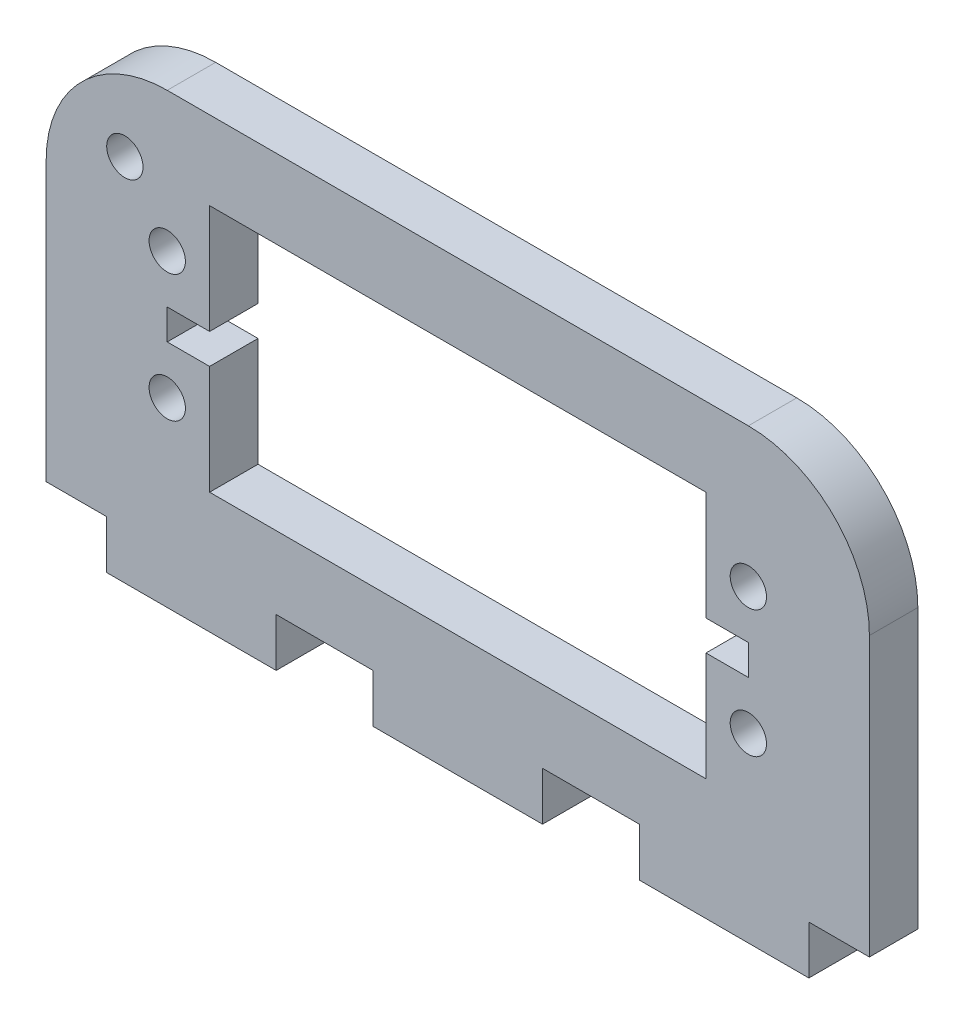
SolidWorks part; units mm, degrees
material "Beech"
ref_plane "Front Plane" through (0, 0, 0) normal (0, 0, 1) x (1, 0, 0)
ref_plane "Top Plane" through (0, 0, 0) normal (0, 1, 0) x (1, 0, 0)
ref_plane "Right Plane" through (0, 0, 0) normal (1, 0, 0) x (0, 0, -1)
sketch "Sketch1" plane through (0, 0, 0) normal (0, 0, 1) x (1, 0, 0)
  line L0 (49, 4) -> (49, 0)
  line L1 (19, 4) -> (19, 0)
  line L2 (41, 4) -> (41, 0)
  line L3 (41, 0) -> (27, 0)
  line L4 (27, 0) -> (27, 4)
  line L5 (63, 0) -> (49, 0)
  line L6 (19, 0) -> (5, 0)
  line L7 (63, 4) -> (63, 0)
  line L8 (5, 4) -> (5, 0)
  line L9 (63, 4) -> (68, 4)
  line L10 (5, 4) -> (0, 4)
  line L11 (54.5, 30.5) -> (54.5, 21.5)
  line L12 (13.5, 30.5) -> (54.5, 30.5)
  line L13 (13.5, 10) -> (13.5, 19)
  line L14 (54.5, 10) -> (13.5, 10)
  line L15 (10, 21.5) -> (10, 19)
  line L16 (10, 19) -> (13.5, 19)
  line L17 (10, 21.5) -> (13.5, 21.5)
  line L18 (58, 21.5) -> (58, 19)
  line L19 (58, 19) -> (54.5, 19)
  line L20 (58, 21.5) -> (54.5, 21.5)
  line L21 (54.5, 19) -> (54.5, 10)
  line L22 (13.5, 21.5) -> (13.5, 30.5)
  line L23 (19, 4) -> (27, 4)
  line L24 (41, 4) -> (49, 4)
  line L25 (68, 4) -> (68, 27)
  line L26 (58, 37) -> (10, 37)
  line L27 (0, 27) -> (0, 4)
  circle A0 centre (10, 15) radius 1.5
  circle A1 centre (10, 25.5) radius 1.5
  circle A2 centre (58, 15) radius 1.5
  circle A3 centre (58, 25.5) radius 1.5
  arc A4 (68, 27) -> (58, 37) centre (58, 27) ccw
  arc A5 (10, 37) -> (0, 27) centre (10, 27) ccw
  circle A6 centre (6.5, 30.5) radius 1.5
extrude "Boss-Extrude1" add sketch "Sketch1" along normal blind 4
